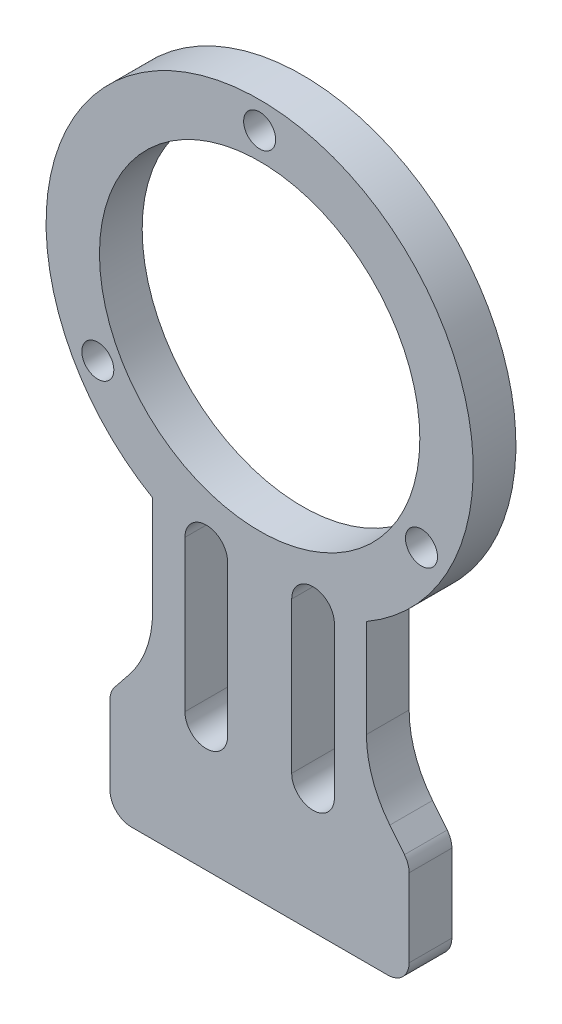
SolidWorks part; units mm, degrees
ref_plane "Front Plane" through (0, 0, 0) normal (0, 0, 1) x (1, 0, 0)
ref_plane "Top Plane" through (0, 0, 0) normal (0, 1, 0) x (1, 0, 0)
ref_plane "Right Plane" through (0, 0, 0) normal (1, 0, 0) x (0, 0, -1)
sketch "Sketch1" plane through (0, 0, 0) normal (0, 0, 1) x (1, 0, 0)
  line L1 (12.1913, -32.7391) -> (13.5617, -34.4522)
  line L2 (14, -35.7016) -> (14, -43)
  line L3 (12, -45) -> (-12.0182, -45)
  line L5 (-14.0182, -35.691) -> (-14.0182, -43)
  line L6 (-12.2095, -32.7286) -> (-13.58, -34.4416)
  line L8 (-10.0182, -17.31) -> (-10.0182, -26.4817)
  line L9 (10, -17.3205) -> (10, -26.4922)
  line L11 (-5, -19) -> (-5, -33.1393) construction
  line L12 (-3, -19) -> (-3, -33.1393)
  line L13 (-7, -19) -> (-7, -33.1393)
  line L14 (5, -19) -> (5, -33.1393) construction
  line L15 (3, -19) -> (3, -33.1393)
  line L16 (7, -19) -> (7, -33.1393)
  arc A0 (10, -17.3205) -> (-10.0182, -17.31) centre (0, 0) ccw
  circle A1 centre (0, 0) radius 15
  arc A2 (10, -26.4922) -> (12.1913, -32.7391) centre (20, -26.4922) ccw
  arc A3 (-12.2095, -32.7286) -> (-10.0182, -26.4817) centre (-20.0182, -26.4817) ccw
  arc A4 (-14.0182, -35.691) -> (-13.58, -34.4416) centre (-12.0182, -35.691) cw
  arc A5 (14, -35.7016) -> (13.5617, -34.4522) centre (12, -35.7016) ccw
  arc A6 (12, -45) -> (14, -43) centre (12, -43) ccw
  arc A7 (-12.0182, -45) -> (-14.0182, -43) centre (-12.0182, -43) cw
  circle A8 centre (0, 17.5) radius 1.5
  circle A9 centre (15.1554, -8.75) radius 1.5
  circle A10 centre (-15.1554, -8.75) radius 1.5
  arc A13 (-3, -19) -> (-7, -19) centre (-5, -19) ccw
  arc A14 (-7, -33.1393) -> (-3, -33.1393) centre (-5, -33.1393) ccw
  arc A15 (3, -19) -> (7, -19) centre (5, -19) cw
  arc A16 (7, -33.1393) -> (3, -33.1393) centre (5, -33.1393) cw
  point P12 (10, -30)
  point P20 (14, -35)
  point P34 (0, 0)
  point P36 (-5, -26.0697)
  point P43 (5, -26.0697)
  dimension "D1" = 30
  dimension "D4" = 10
  dimension "D5" = 2
  dimension "D6" = 2
  dimension "D7" = 2
  dimension "D8" = 17.5
  dimension "D2" = 45
  dimension "D3" = 5
  dimension "D11" = 26
  dimension "D9" = 3
extrude "Boss-Extrude1" add sketch "Sketch1" along normal blind 4
sketch "Sketch2" plane through (0, -45, 0) normal (0, -1, 0) x (1, 0, 0)
  line L1 (-12.0182, 0) -> (12, 0) construction
  circle A0 centre (-10.0091, 2) radius 1
  circle A1 centre (9.9909, 2) radius 1
  point P2 (-0.0091, 0)
  dimension "D1" = 10
  dimension "D2" = 2
  dimension "D3" = 20
extrude "Cut-Extrude1" cut sketch "Sketch2" against normal blind 4
